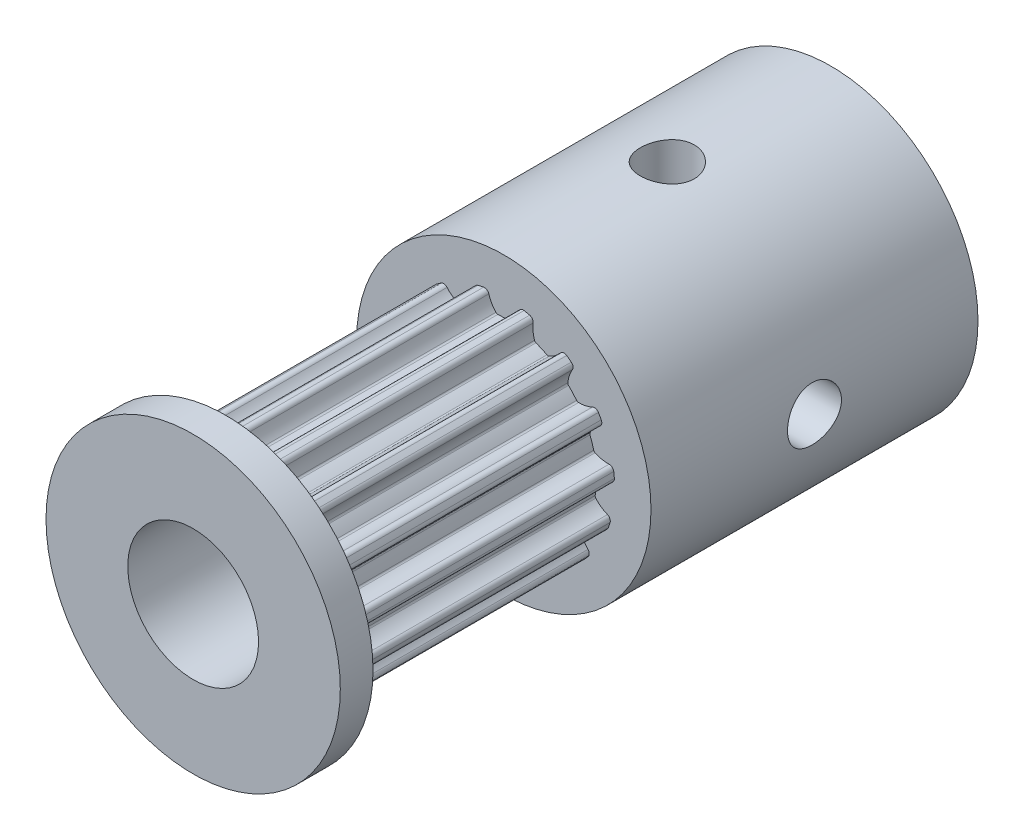
SolidWorks part; units mm, degrees
material "6061-T6 (SS)"
ref_plane "前基準面" through (0, 0, 0) normal (0, 0, 1) x (1, 0, 0)
ref_plane "上基準面" through (0, 0, 0) normal (0, 1, 0) x (1, 0, 0)
ref_plane "右基準面" through (0, 0, 0) normal (1, 0, 0) x (0, 0, -1)
sketch "草圖1" plane through (0, 0, 0) normal (0, 0, 1) x (1, 0, 0)
  circle A0 centre (0, 0) radius 6.78
  dimension "D1" = 13.56
extrude "填料-伸長1" add sketch "草圖1" along normal mid plane 17
sketch "草圖2" plane through (0, 0, 8.5) normal (0, 0, 1) x (1, 0, 0)
  line L0 (0, 0) -> (0, 7.034) construction
  line L1 (-0.975, 7.034) -> (0.975, 7.034) construction
  arc A0 (-0.367, 5.6581) -> (0.367, 5.6581) centre (0, 0) cw
  circle A1 centre (0, 0) radius 6.78 construction
  arc A2 (-1.2374, 6.6661) -> (-0.918, 6.4707) centre (-1.1863, 6.3908) cw
  arc A3 (-0.918, 6.4707) -> (-0.4878, 5.707) centre (0.975, 7.034) ccw
  arc A4 (-0.4878, 5.707) -> (-0.367, 5.6581) centre (-0.3767, 5.8078) ccw
  arc A5 (0.4878, 5.707) -> (0.367, 5.6581) centre (0.3767, 5.8078) cw
  arc A6 (0.918, 6.4707) -> (0.4878, 5.707) centre (-0.975, 7.034) cw
  arc A7 (1.2374, 6.6661) -> (0.918, 6.4707) centre (1.1863, 6.3908) ccw
  point P6 (0, 5.67)
  point P18 (0, 6.78)
  dimension "D1" = 1.11
  dimension "D2" = 0.15
  dimension "D3" = 1.975
  dimension "D4" = 0.28
  dimension "D5" = 1.95
  dimension "D6" = 0.254
extrude "除料-伸長1" cut sketch "草圖2" against normal through all and the other way through all flip side to cut
pattern_circular "環狀複製排列1" count 15 over 360 about axis through (0, 0, 8.5) along (0, 0, 1) of "除料-伸長1"
sketch "草圖3" plane through (0, 0, 8.5) normal (0, 0, 1) x (1, 0, 0)
  circle A0 centre (0, 0) radius 9
  dimension "D1" = 18
extrude "填料-伸長2" add sketch "草圖3" along normal blind 2
sketch "草圖5" plane through (0, 0, -8.5) normal (0, 0, -1) x (-1, 0, 0)
  circle A0 centre (0, 0) radius 9
  circle A1 centre (0, 0) radius 9 construction
extrude "填料-伸長3" add sketch "草圖5" along normal blind 20
sketch "草圖4" plane through (0, 0, 10.5) normal (0, 0, 1) x (1, 0, 0)
  circle A0 centre (0, 0) radius 4
  dimension "D1" = 8
extrude "除料-伸長2" cut sketch "草圖4" against normal through all
hole_wizard "M4x0.7 螺紋孔1" positions "草圖6" profile "草圖7" tap size "M4x0.7" standard "Ansi Metric"
sketch "草圖6" plane through (0, 0, 0) normal (0, 1, 0) x (1, 0, 0)
  line L0 (0, 28.5) -> (0, 8.5) construction
  line L1 (4, 28.5) -> (-4, 28.5) construction
  line L2 (-0.367, 8.5) -> (0.367, 8.5) construction
  point P11 (0, 18.5)
sketch "草圖7" plane through (0, 0, -18.5) normal (1, 0, 0) x (0, 0, -1)
  line L0 (0, 0) -> (0, 9)
  line L1 (0, 9) -> (1.65, 9)
  line L2 (1.65, 9) -> (1.65, 0)
  line L5 (1.65, 0) -> (0, 0)
  line L11 (0, -6.35) -> (0, 107.95) construction
  dimension "貫穿螺孔鑽直徑" = 3.3
  dimension "貫穿螺孔鑽深度" = 9
pattern_circular "環狀複製排列2" count 2 every 90 about axis through (0, 0, -28.5) along (0, 0, -1) of "M4x0.7 螺紋孔1"
